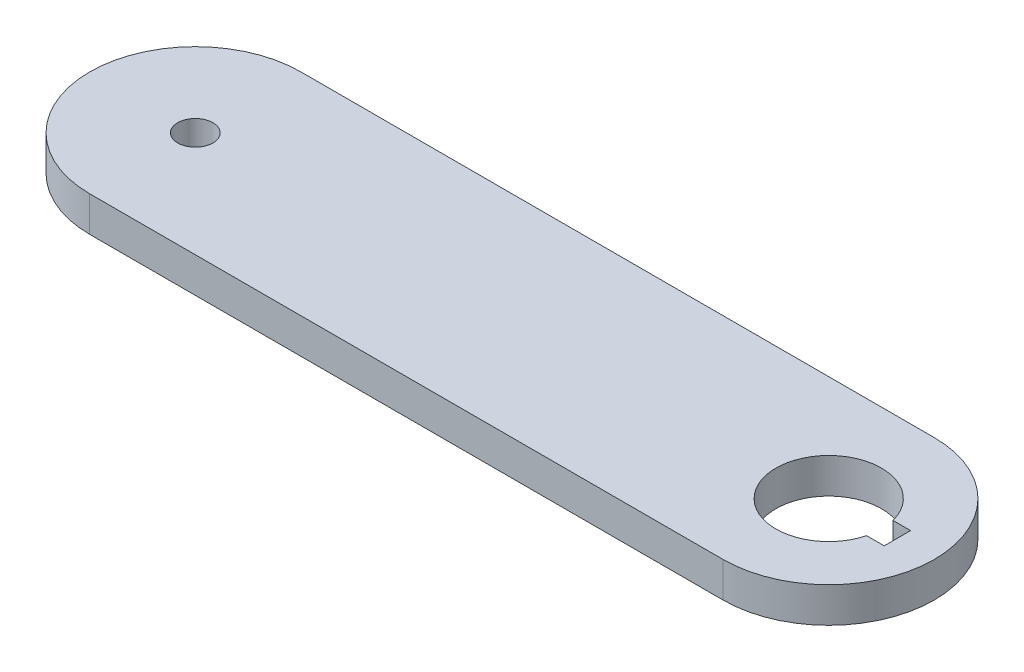
SolidWorks part; units mm, degrees
ref_plane "Front Plane" through (0, 0, 0) normal (0, 0, 1) x (1, 0, 0)
ref_plane "Top Plane" through (0, 0, 0) normal (0, 1, 0) x (1, 0, 0)
ref_plane "Right Plane" through (0, 0, 0) normal (1, 0, 0) x (0, 0, -1)
sketch "Sketch1" plane through (0, 0, 0) normal (0, 1, 0) x (1, 0, 0)
  line L0 (0, 0) -> (114.3, 0) construction
  line L1 (0, 19.05) -> (114.3, 19.05)
  line L2 (0, -19.05) -> (114.3, -19.05)
  line L3 (114.3, 0) -> (137.0959, 0) construction
  line L5 (123.5225, -2.3813) -> (126.6975, -2.3813)
  line L7 (123.5225, 2.3813) -> (126.6975, 2.3813)
  line L8 (126.6975, -2.3813) -> (126.6975, 2.3813)
  arc A0 (0, 19.05) -> (0, -19.05) centre (0, 0) ccw
  arc A1 (114.3, -19.05) -> (114.3, 19.05) centre (114.3, 0) ccw
  arc A2 (123.5225, 2.3813) -> (123.5225, -2.3813) centre (114.3, 0) ccw
  point P3 (57.15, 0)
  point P9 (126.6975, 0)
  point P15 (0, 0)
  point P16 (0, 0)
  point P18 (0, 0)
  point P19 (0, 0)
  dimension "D2" = 19.05
  dimension "D3" = 19.05
  dimension "D1" = 114.3
  dimension "D4" = 4.7625
  dimension "D5" = 3.175
  dimension "D6" = 12.3975
extrude "Boss-Extrude1" add sketch "Sketch1" along normal blind 6.35
sketch "Sketch3" plane through (0, 6.35, 0) normal (0, 1, 0) x (1, 0, 0)
  circle A0 centre (0, 0) radius 3.175
  dimension "D1" = 6.35
extrude "Cut-Extrude1" cut sketch "Sketch3" against normal through all
